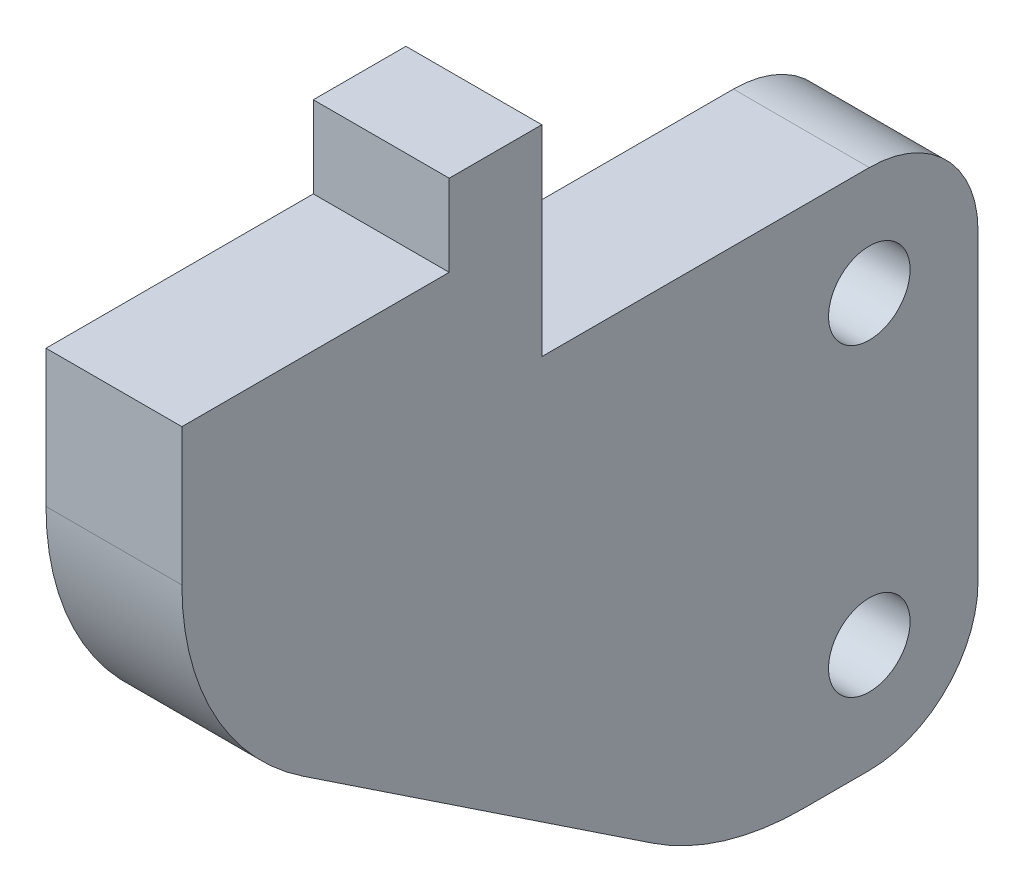
SolidWorks part; units mm, degrees
ref_plane "Front Plane" through (0, 0, 0) normal (0, 0, 1) x (1, 0, 0)
ref_plane "Top Plane" through (0, 0, 0) normal (0, 1, 0) x (1, 0, 0)
ref_plane "Right Plane" through (0, 0, 0) normal (1, 0, 0) x (0, 0, -1)
sketch "Sketch1" plane through (0, 0, 0) normal (1, 0, 0) x (0, 0, -1)
  line L0 (19.456, 26.1832) -> (149.456, 26.1832) construction
  line L1 (80.8457, 85.158) -> (80.8457, 73.9445)
  line L2 (76.8457, 89.158) -> (64.7949, 89.158)
  line L3 (64.7949, 89.158) -> (64.7949, 96.5477)
  line L4 (64.7949, 96.5477) -> (61.387, 96.5477)
  line L5 (61.387, 96.5477) -> (61.387, 93.5477)
  line L6 (61.387, 93.5477) -> (51.5504, 93.5477)
  line L7 (51.5504, 93.5477) -> (51.5504, 88.5035)
  line L8 (76.8457, 69.9445) -> (74.4034, 69.9445)
  line L9 (68.8607, 71.6211) -> (56.0077, 80.1801)
  circle A0 centre (76.8457, 85.158) radius 1.5
  circle A1 centre (76.8457, 73.9445) radius 1.5
  circle A2 centre (76.8457, 85.158) radius 4
  circle A3 centre (76.8457, 73.9445) radius 4
  arc A4 (74.4034, 69.9445) -> (68.8607, 71.6211) centre (74.4034, 79.9445) cw
  arc A5 (51.5504, 88.5035) -> (56.0077, 80.1801) centre (61.5504, 88.5035) ccw
  dimension "D2" = 3
  dimension "D3" = 3
  dimension "D4" = 8
  dimension "D5" = 8
  dimension "D7" = 10
  dimension "D1" = 130
  dimension "D6" = 3
extrude "Boss-Extrude1" add sketch "Sketch1" along normal blind 5 contours A3 A1 | A2 A0 | L7 A5 L9 A4 L8 A3 L1 A2 L2 L3 L4 L5 L6
